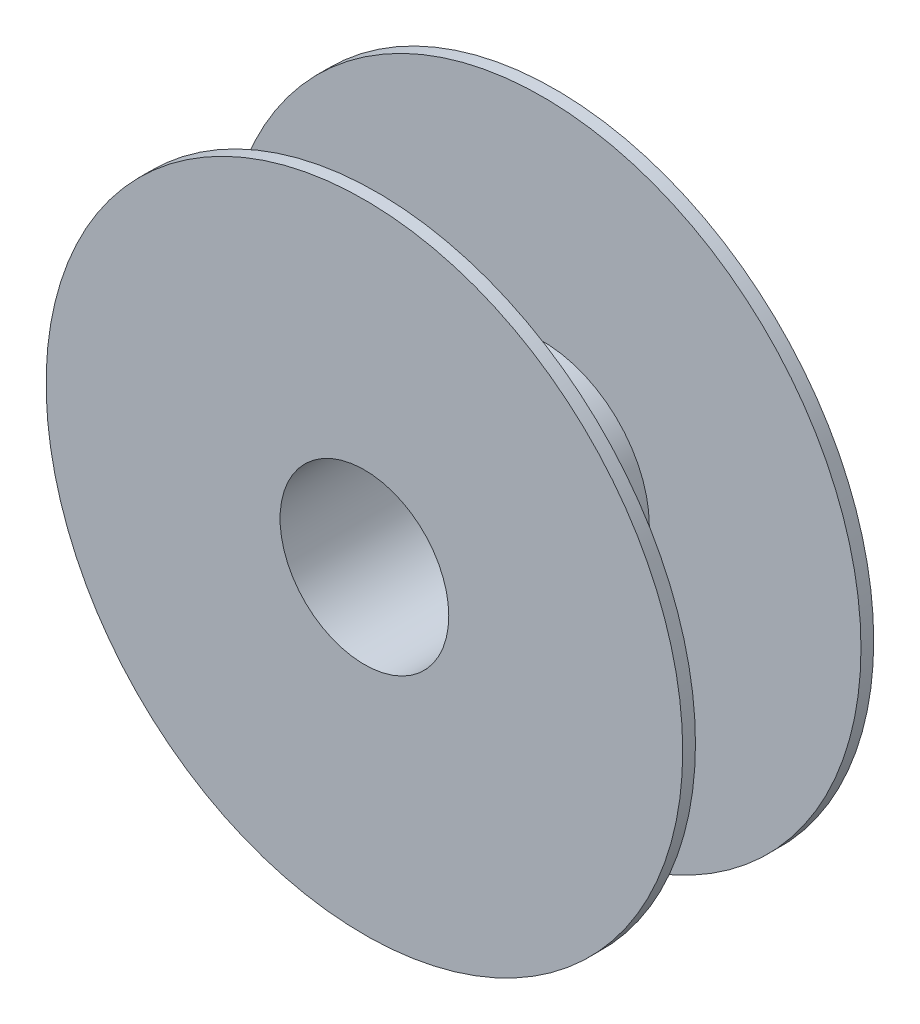
SolidWorks part; units mm, degrees
ref_plane "Front Plane" through (0, 0, 0) normal (0, 0, 1) x (1, 0, 0)
ref_plane "Top Plane" through (0, 0, 0) normal (0, 1, 0) x (1, 0, 0)
ref_plane "Right Plane" through (0, 0, 0) normal (1, 0, 0) x (0, 0, -1)
sketch "Sketch1" plane through (0, 0, 0) normal (0, 0, 1) x (1, 0, 0)
  circle A0 centre (0, 0) radius 26.5
  circle A2 centre (0, 0) radius 100
  dimension "D1" = 200
  dimension "D3" = 53
extrude "Boss-Extrude1" add sketch "Sketch1" along normal mid plane 60 contours A2 A0
sketch "Sketch2" plane through (0, 0, 0) normal (0, 0, 1) x (1, 0, 0)
  circle A0 centre (0, 0) radius 33.5
  circle A1 centre (0, 0) radius 100
  circle A4 centre (0, 0) radius 26.5 construction
  point P8 (7.1682, 25.5121)
  point P9 (13.6912, 22.6892)
  dimension "D1" = 200
  dimension "D2" = 7
extrude "Cut-Extrude1" cut sketch "Sketch2" against normal mid plane 52
